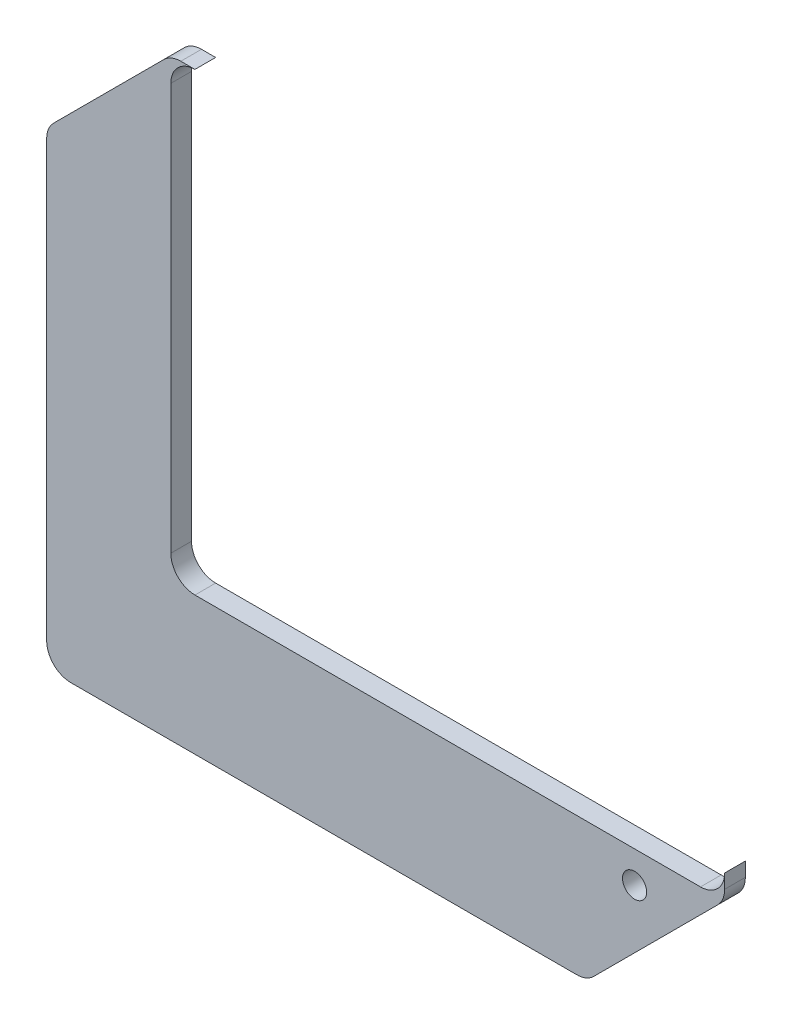
SolidWorks part; units mm, degrees
material "Acrylic (Medium-high impact)"
ref_plane "Front Plane" through (0, 0, 0) normal (0, 0, 1) x (1, 0, 0)
ref_plane "Top Plane" through (0, 0, 0) normal (0, 1, 0) x (1, 0, 0)
ref_plane "Right Plane" through (0, 0, 0) normal (1, 0, 0) x (0, 0, -1)
sketch "Sketch1" plane through (0, 0, 0) normal (0, 0, 1) x (1, 0, 0)
  line L0 (0, 66) -> (-18, 48)
  line L1 (0, 0) -> (80.3, 0)
  line L2 (0, 0) -> (0, 66)
  line L3 (0, 66) -> (80.3, 66)
  line L4 (80.3, 0) -> (80.3, 66)
  line L5 (-18, 48) -> (-18, -20)
  line L6 (-18, -20) -> (60.3, -20)
  line L7 (60.3, -20) -> (80.3, 0)
  dimension "D1" = 80.3
  dimension "D2" = 66
  dimension "D3" = 20
  dimension "D4" = 18
  dimension "D5" = 45
  dimension "D6" = 45
extrude "Boss-Extrude1" add sketch "Sketch1" along normal blind 3 contours L6 L7 L1 L2 L0 L5 | L1 L4 L3 L2
fillet "Fillet1" radius 3.5 6 edges at (80.3, 0, 1.5) (60.3, -20, 1.5) (-18, -20, 1.5) (-18, 48, 1.5) (80.3, 66, 1.5) (0, 66, 1.5)
sketch "Sketch2" plane through (0, 0, 3) normal (0, 0, 1) x (1, 0, 0)
  line L0 (1.4497, 66) -> (76.8, 66) construction
  line L1 (0, 0) -> (80.3, 0)
  line L2 (0, 0) -> (0, 66)
  line L3 (0, 66) -> (80.3, 66)
  line L4 (80.3, 0) -> (80.3, 66)
  line L5 (80.3, 1.4497) -> (80.3, 62.5) construction
  circle A0 centre (3.5, 62.5) radius 3.5
  circle A1 centre (76.8, 62.5) radius 3.5
  circle A2 centre (76.8, 3.5) radius 3.5
  arc M4 (80.3, 62.5) -> (76.8, 66) centre (76.8, 62.5) ccw
  line M5 (76.8, 66) -> (1.4497, 66)
  dimension "D1" = 7
  dimension "D2" = 7
  dimension "D3" = 7
extrude "Cut-Extrude1" cut sketch "Sketch2" against normal through all contours A2 L4 A1 A0 L2 L1 M5 | A0 | A1 M4 | A2
fillet "Fillet2" radius 3.5 1 edges at (0, 0, 1.5)
hole_wizard "Ø3.5 (3.5) Diameter Hole1" positions "Sketch4" profile "Sketch3" hole size "Ø3.5" standard "ANSI Metric" end condition through all
sketch "Sketch4" plane through (0, 0, 3) normal (0, 0, 1) x (1, 0, 0)
  line L2 (-14.5, -20) -> (58.8503, -20) construction
  point P0 (67.24, -4.57)
  dimension "D1" = 15.43
  dimension "D2" = 13.06
sketch "Sketch3" plane through (67.24, -4.57, 3) normal (1, 0, 0) x (0, -1, 0)
  line L0 (0, 0) -> (0, 3)
  line L1 (0, 3) -> (1.75, 3)
  line L2 (1.75, 3) -> (1.75, 0)
  line L5 (1.75, 0) -> (0, 0)
  line L11 (0, -6.35) -> (0, 107.95) construction
  dimension "Thru Hole Dia." = 3.5
  dimension "Thru Hole Depth" = 3
